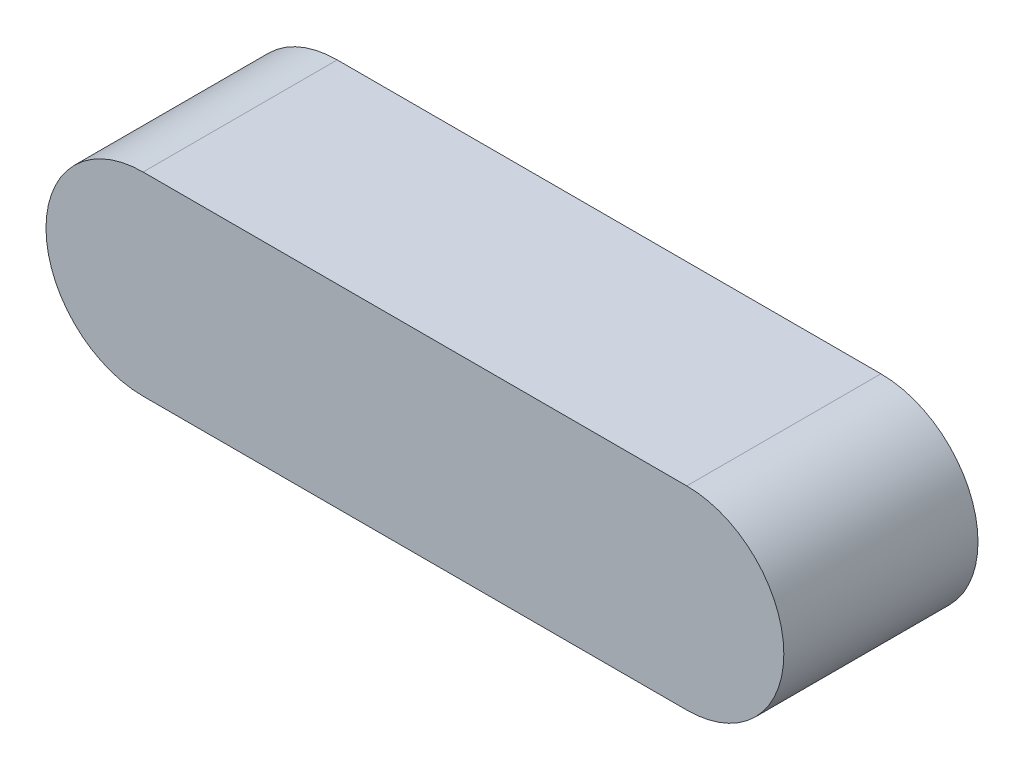
SolidWorks part; units mm, degrees
ref_plane "前视基准面" through (0, 0, 0) normal (0, 0, 1) x (1, 0, 0)
ref_plane "上视基准面" through (0, 0, 0) normal (0, 1, 0) x (1, 0, 0)
ref_plane "右视基准面" through (0, 0, 0) normal (1, 0, 0) x (0, 0, -1)
sketch "草图1" plane through (0, 0, 0) normal (0, 0, 1) x (1, 0, 0)
  line L1 (-7, 2.5) -> (7, 2.5)
  line L2 (-7, 2.5) -> (-7, -2.5)
  line L3 (-7, -2.5) -> (7, -2.5)
  line L4 (7, 2.5) -> (7, -2.5)
  line L5 (-7, 2.5) -> (7, -2.5) construction
  line L6 (-7, -2.5) -> (7, 2.5) construction
  arc A0 (7, 2.5) -> (7, -2.5) centre (7, 0) cw
  arc A1 (-7, 2.5) -> (-7, -2.5) centre (-7, 0) ccw
  point P0 (0, 0)
  dimension "D1" = 14
  dimension "D2" = 5
extrude "凸台-拉伸1" add sketch "草图1" along normal blind 5 contours L2 A1 | L4 L1 L2 L3 | A0 L4
